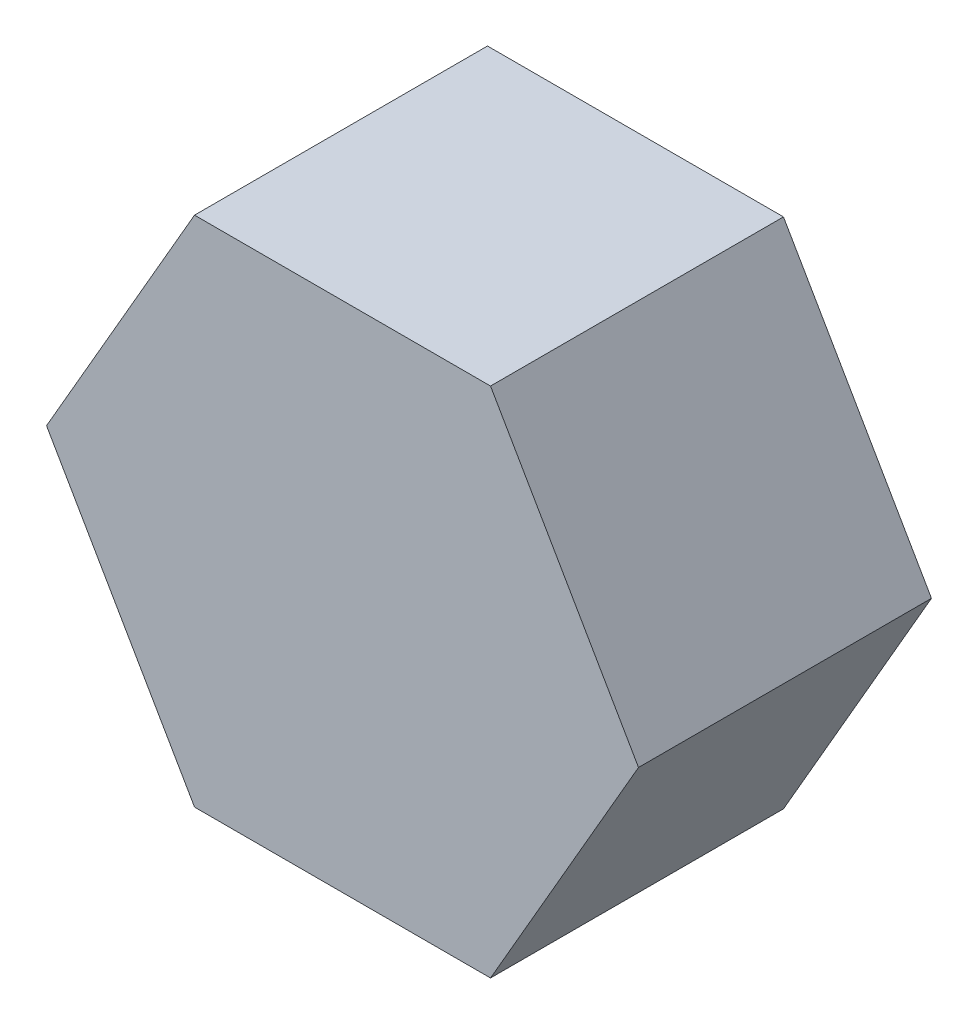
SolidWorks part; units mm, degrees
ref_plane "Front Plane" through (0, 0, 0) normal (0, 0, 1) x (1, 0, 0)
ref_plane "Top Plane" through (0, 0, 0) normal (0, 1, 0) x (1, 0, 0)
ref_plane "Right Plane" through (0, 0, 0) normal (1, 0, 0) x (0, 0, -1)
sketch "Sketch1" plane through (0, 0, 0) normal (0, 0, 1) x (1, 0, 0)
  line L1 (-8.0829, 0) -> (-4.0415, -7)
  line L2 (-4.0415, -7) -> (4.0415, -7)
  line L3 (4.0415, -7) -> (8.0829, 0)
  line L4 (8.0829, 0) -> (4.0415, 7)
  line L5 (4.0415, 7) -> (-4.0415, 7)
  line L6 (-4.0415, 7) -> (-8.0829, 0)
  circle A0 centre (0, 0) radius 7 construction
  dimension "D2" = 14
extrude "Boss-Extrude1" add sketch "Sketch1" along normal blind 8
